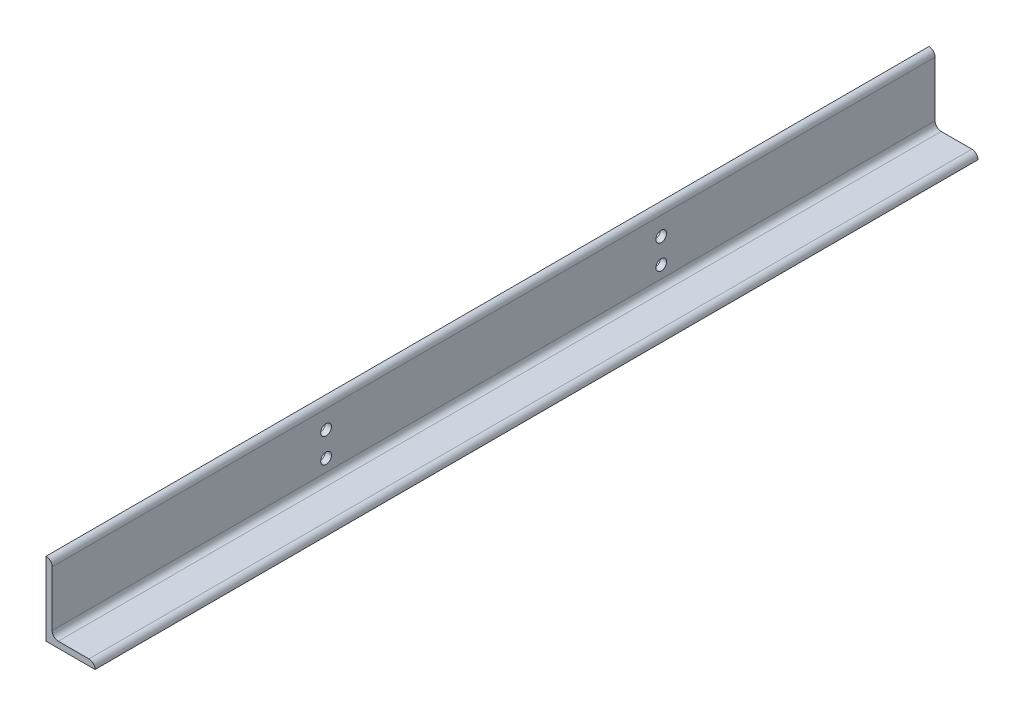
SolidWorks part; units mm, degrees
ref_plane "Front Plane" through (0, 0, 0) normal (0, 0, 1) x (1, 0, 0)
ref_plane "Top Plane" through (0, 0, 0) normal (0, 1, 0) x (1, 0, 0)
ref_plane "Right Plane" through (0, 0, 0) normal (1, 0, 0) x (0, 0, -1)
sketch "Sketch1" plane through (0, 0, 0) normal (0, 0, 1) x (1, 0, 0)
  line L0 (0, 0) -> (0, 152.4)
  line L1 (0, 152.4) -> (0.0051, 152.4)
  line L2 (12.7, 139.7051) -> (12.7, 25.4)
  line L3 (25.4, 12.7) -> (88.9051, 12.7)
  line L4 (101.6, 0.0051) -> (101.6, 0)
  line L5 (101.6, 0) -> (0, 0)
  arc A0 (101.6, 0.0051) -> (88.9051, 12.7) centre (88.9051, 0.0051) ccw
  arc A1 (0.0051, 152.4) -> (12.7, 139.7051) centre (0.0051, 139.7051) cw
  arc A2 (25.4, 12.7) -> (12.7, 25.4) centre (25.4, 25.4) cw
  circle A3 centre (0, 0) radius 12.7 construction
  dimension "D2" = 0.0051
  dimension "Radius_1" = 12.7
  dimension "Radius_2" = 12.7
  dimension "D1" = 12.7
  dimension "V_leg" = 152.4
  dimension "H_leg" = 101.6
  dimension "Thickness" = 12.7
  dimension "Flat_wid" = 0.0051
extrude "Boss-Extrude1" add sketch "Sketch1" along normal mid plane 1828.8
sketch "Sketch2" plane through (0, 0, 0) normal (-1, 0, 0) x (0, 0, 1)
  line L0 (914.4, 152.4) -> (914.4, 0) construction
  line L1 (346.964, 50.8) -> (346.964, 101.7919) construction
  line L2 (914.4, 0) -> (-914.4, 0) construction
  line L3 (-347.218, 50.8) -> (-347.218, 101.6) construction
  circle A0 centre (346.964, 50.8) radius 11.1125
  circle A1 centre (-347.218, 50.8) radius 11.1125
  circle A2 centre (346.964, 101.7919) radius 11.1125
  circle A3 centre (-347.218, 101.6) radius 11.1125
  dimension "D1" = 22.225
  dimension "D3" = 694.182
  dimension "D4" = 50.8
  dimension "D5" = 50.8
  dimension "D6" = 22.225
  dimension "D7" = 22.225
  dimension "D2" = 567.436
extrude "Cut-Extrude1" cut sketch "Sketch2" against normal up to next
equation "\"D5@Sketch2\" = \"D4@Sketch2\""
